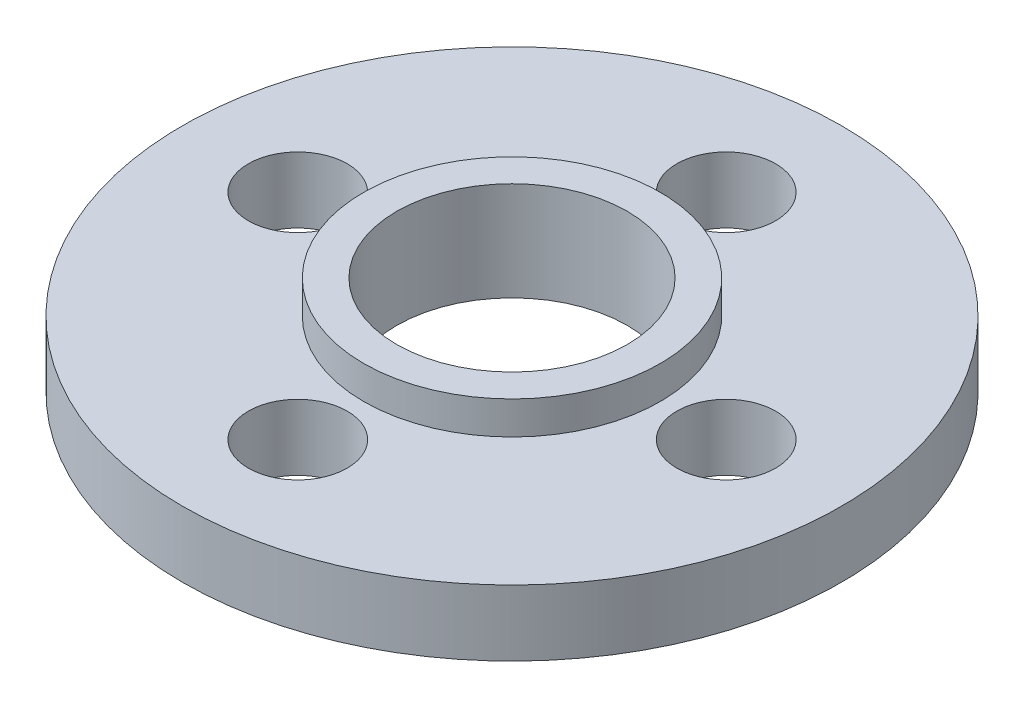
SolidWorks part; units mm, degrees
ref_plane "前视基准面" through (0, 0, 0) normal (0, 0, 1) x (1, 0, 0)
ref_plane "上视基准面" through (0, 0, 0) normal (0, 1, 0) x (1, 0, 0)
ref_plane "右视基准面" through (0, 0, 0) normal (1, 0, 0) x (0, 0, -1)
sketch "草图1" plane through (0, 0, 0) normal (0, 1, 0) x (1, 0, 0)
  circle A0 centre (0, 0) radius 10
  circle A1 centre (0, 0) radius 3.5
  circle A2 centre (0, 6.5) radius 1.5
  circle A3 centre (0, -6.5) radius 1.5
  circle A4 centre (-6.5, 0) radius 1.5
  circle A5 centre (6.5, 0) radius 1.5
extrude "凸台-拉伸1" add sketch "草图1" along normal blind 3
sketch "草图2" plane through (0, 3, 0) normal (0, 1, 0) x (1, 0, 0)
  circle A0 centre (0, 0) radius 4.5
  circle A1 centre (0, 0) radius 10
  circle A2 centre (0, -6.5) radius 1.5
  circle A3 centre (0, 6.5) radius 1.5
  circle A4 centre (6.5, 0) radius 1.5
  circle A5 centre (-6.5, 0) radius 1.5
extrude "切除-拉伸1" cut sketch "草图2" against normal blind 1
sketch "草图3" plane through (0, 0, 0) normal (0, -1, 0) x (-1, 0, 0)
  line L0 (0, -6.5) -> (0, 0)
